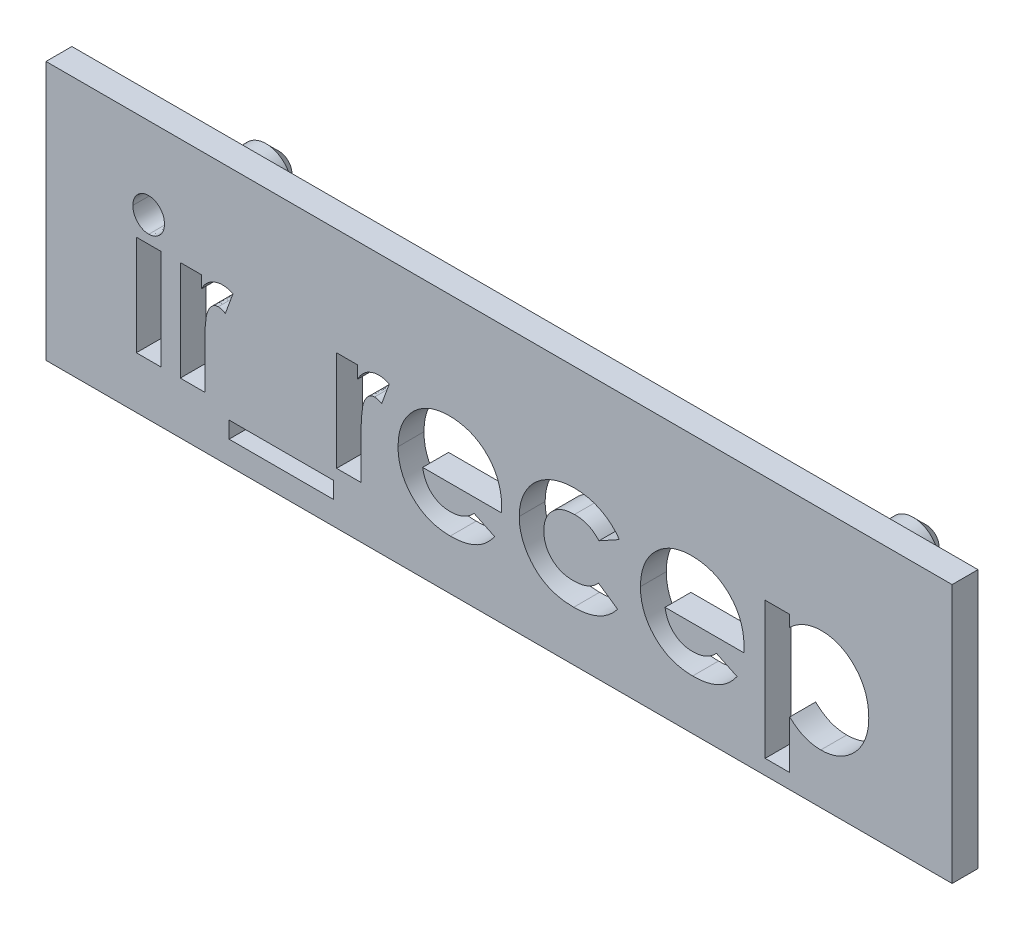
SolidWorks part; units mm, degrees
ref_plane "Plan de face" through (0, 0, 0) normal (0, 0, 1) x (1, 0, 0)
ref_plane "Plan de dessus" through (0, 0, 0) normal (0, 1, 0) x (1, 0, 0)
ref_plane "Plan de droite" through (0, 0, 0) normal (1, 0, 0) x (0, 0, -1)
sketch "Esquisse1" plane through (0, 0, 0) normal (0, 0, 1) x (1, 0, 0)
  line L1 (0, 0) -> (35, 0)
  line L2 (0, 0) -> (0, -10)
  line L3 (0, -10) -> (35, -10)
  line L4 (35, 0) -> (35, -10)
  dimension "D1" = 35
  dimension "D2" = 10
extrude "Boss.-Extru.1" add sketch "Esquisse1" along normal blind 1
sketch "Esquisse2" plane through (0, 0, 0) normal (0, 0, -1) x (-1, 0, 0)
  line L0 (-35, 0) -> (0, 0) construction
  line L1 (-35, -10) -> (-35, 0) construction
  line L2 (0, 0) -> (0, -10) construction
  circle A0 centre (-30, -3) radius 1
  circle A1 centre (-5, -3) radius 1
  dimension "D4" = 2
  dimension "D1" = 3
  dimension "D2" = 5
  dimension "D3" = 5
extrude "Boss.-Extru.2" add sketch "Esquisse2" along normal blind 3
chamfer "Chanfrein1" distance 0.5 angle 45 2 edges at (29, -3, -3) (4, -3, -3)
sketch "Esquisse3" plane through (0, 0, 1) normal (0, 0, 1) x (1, 0, 0)
  line L0 (2.5, -8) -> (32.5, -8) construction
  line L3 (0, -10) -> (35, -10) construction
  line L4 (0, 0) -> (0, -10) construction
  line L5 (35, -10) -> (35, 0) construction
  text T1 "<b>ir_recep</b>" font "Century Gothic" height in points 20
  point P12 (32.5, -8)
  dimension "D1" = 2
  dimension "D2" = 2.5
  dimension "D3" = 30
  dimension "D4" = 2.5
extrude "Enlèv. mat.-Extru.2" cut sketch "Esquisse3" against normal blind 1
sketch "Esquisse4" plane through (0, 0, 1) normal (0, 0, 1) x (1, 0, 0)
  line L8 (7.072, -9.0998) -> (11.1033, -9.0998)
  line L9 (7.072, -8.4606) -> (7.072, -9.0998)
  line L10 (11.1033, -8.4606) -> (7.072, -8.4606)
  line L11 (11.1033, -9.0998) -> (11.1033, -8.4606)
  line L12 (7.072, -9.0998) -> (11.1033, -9.0998)
  line L13 (7.072, -8.4606) -> (7.072, -9.0998)
  line L14 (11.1033, -8.4606) -> (7.072, -8.4606)
  line L15 (11.1033, -9.0998) -> (11.1033, -8.4606)
  dimension "D1" = 0.15
extrude "Enlèv. mat.-Extru.3" cut sketch "Esquisse4" against normal through all
